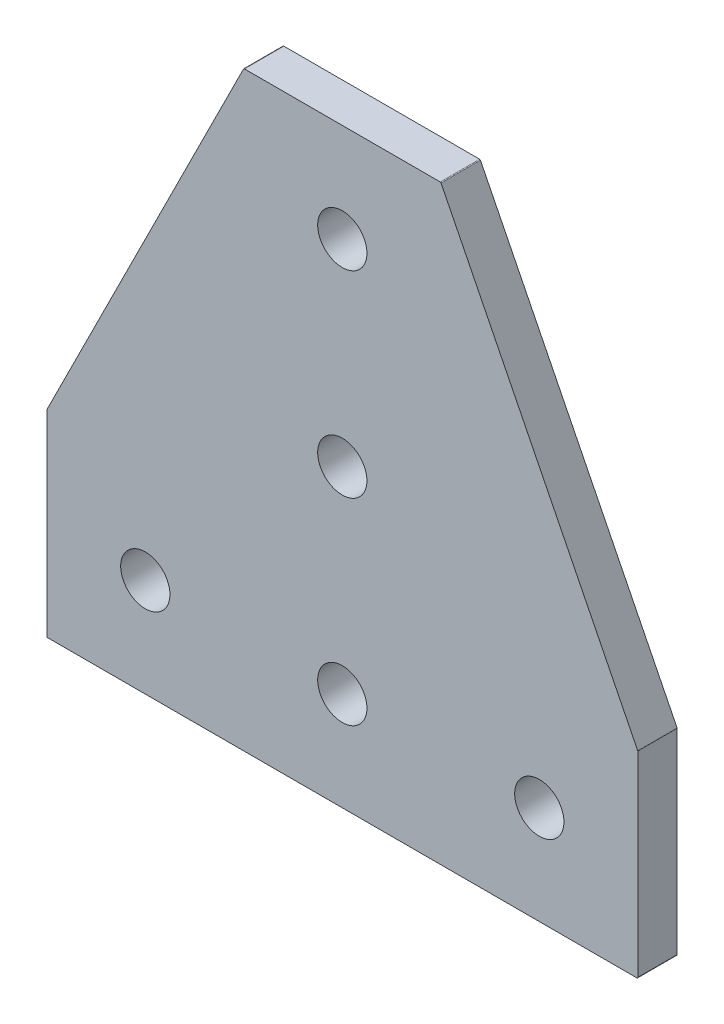
SolidWorks part; units mm, degrees
ref_plane "Front Plane" through (0, 0, 0) normal (0, 0, 1) x (1, 0, 0)
ref_plane "Top Plane" through (0, 0, 0) normal (0, 1, 0) x (1, 0, 0)
ref_plane "Right Plane" through (0, 0, 0) normal (1, 0, 0) x (0, 0, -1)
sketch "Sketch1" plane through (0, 0, 0) normal (0, 0, 1) x (1, 0, 0)
  line L0 (30, 60) -> (30, 0) construction
  line L1 (0, 0) -> (60, 0) construction
  line L2 (0, 0) -> (0, 60) construction
  line L3 (0, 60) -> (60, 60) construction
  line L4 (60, 0) -> (60, 60) construction
  line L5 (0, 20) -> (60, 20) construction
  line L6 (20, 60) -> (40, 60)
  line L7 (20, 60) -> (0, 20)
  line L8 (0, 20) -> (0, 0)
  line L9 (0, 0) -> (60, 0)
  line L10 (60, 0) -> (60, 20)
  line L11 (60, 20) -> (40, 60)
  point P11 (30, 60)
  dimension "D1" = 60
  dimension "D2" = 60
  dimension "D3" = 20
  dimension "D4" = 20
extrude "Boss-Extrude1" add sketch "Sketch1" against normal blind 4
sketch "Sketch2" plane through (0, 0, 0) normal (0, 0, 1) x (1, 0, 0)
  line L0 (60, 0) -> (60, 20) construction
  line L1 (0, 0) -> (60, 0) construction
  circle A0 centre (30, 10) radius 2.5
  point P4 (60, 10)
  point P7 (30, 0)
  dimension "D1" = 5
extrude "Cut-Extrude1" cut sketch "Sketch2" against normal blind 4
pattern_linear "LPattern1" count 3 spacing 20 along (0, 1, 0) of "Cut-Extrude1"
sketch "Sketch3" plane through (0, 0, 0) normal (0, 0, 1) x (1, 0, 0)
  circle A0 centre (10, 10) radius 2.5
  circle A1 centre (50, 10) radius 2.5
  circle A2 centre (30, 10) radius 2.5 construction
  dimension "D1" = 10
  dimension "D2" = 40
extrude "Cut-Extrude2" cut sketch "Sketch3" against normal blind 4
fillet "Fillet1" radius 0.1 6 edges at (0, 0, -2) (0, 20, -2) (20, 60, -2) (60, 0, -2) (60, 20, -2) (40, 60, -2)
